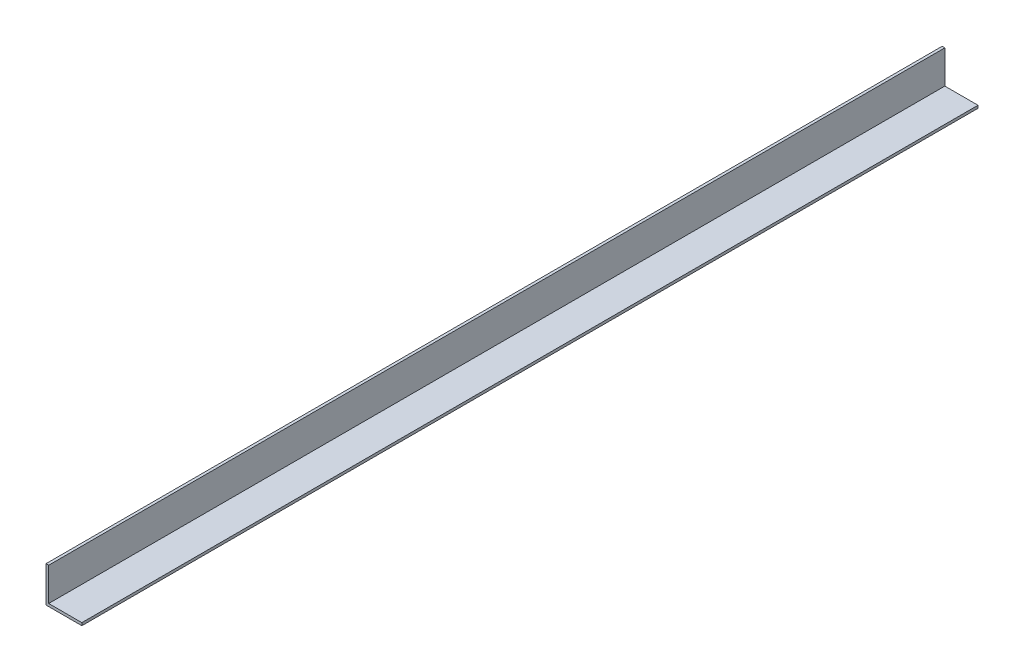
SolidWorks part; units mm, degrees
material "6063 T5"
ref_plane "Спереди" through (0, 0, 0) normal (0, 0, 1) x (1, 0, 0)
ref_plane "Сверху" through (0, 0, 0) normal (0, 1, 0) x (1, 0, 0)
ref_plane "Справа" through (0, 0, 0) normal (1, 0, 0) x (0, 0, -1)
sketch "Эскиз1" plane through (0, 0, 0) normal (0, 0, 1) x (1, 0, 0)
  line L0 (0, 40) -> (0, 0)
  line L1 (0, 0) -> (40, 0)
  line L2 (40, 0) -> (40, 3)
  line L3 (40, 3) -> (3, 3)
  line L4 (3, 3) -> (3, 40)
  line L5 (3, 40) -> (0, 40)
  dimension "D1" = 40
  dimension "D2" = 3
extrude "Бобышка-Вытянуть1" add sketch "Эскиз1" along normal blind 1000
